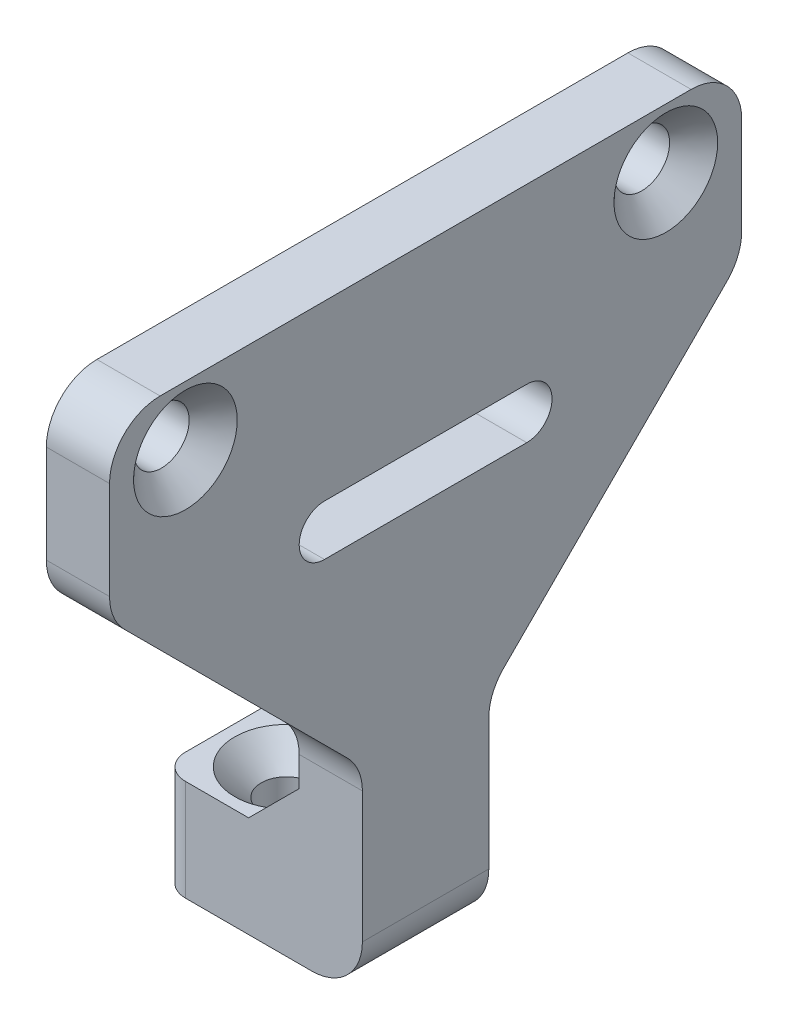
SolidWorks part; units mm, degrees
ref_plane "前视基准面" through (0, 0, 0) normal (0, 0, 1) x (1, 0, 0)
ref_plane "上视基准面" through (0, 0, 0) normal (0, 1, 0) x (1, 0, 0)
ref_plane "右视基准面" through (0, 0, 0) normal (1, 0, 0) x (0, 0, -1)
sketch "草图1" plane through (0, 0, 0) normal (1, 0, 0) x (0, 0, -1)
  line L0 (-12.5, 0) -> (12.5, 0) construction
  line L1 (-12.5, 2.35) -> (12.5, 2.35)
  line L2 (-12.5, 2.35) -> (-12.5, -2.35)
  line L3 (-12.5, -2.35) -> (12.5, -2.35)
  line L4 (12.5, 2.35) -> (12.5, -2.35)
  line L5 (0, -2.35) -> (0, 11.5618) construction
  circle A1 centre (9.5, 0) radius 1.1
  circle A2 centre (-9.5, 0) radius 1.1
  dimension "D3" = 2.2
  dimension "D1" = 9.5
  dimension "D4" = 4.7
  dimension "D5" = 25
  dimension "D6" = 1.9
extrude "凸台-拉伸1" add sketch "草图1" along normal blind 2.5
hole_wizard "M2 平头机械螺钉的锥形沉头孔1" positions "3D草图1" profile "草图2" countersink size "M2" standard "ANSI Metric"
sketch3d "3D草图1"
  line L0 (2.5, 0, 9.5) -> (0, 0, 9.5) construction
  line L1 (2.5, 0, -9.5) -> (0, 0, -9.5) construction
  point P0 (2.5, 0, 9.5)
  point P4 (4.6063, -1.0097, -5.9012)
  point P12 (2.5, 0, -9.5)
sketch "草图2" plane through (2.5, 0, 9.5) normal (0, 1, 0) x (0, 0, -1)
  line L0 (0, 0) -> (0, 2.5)
  line L1 (0, 2.5) -> (1, 2.5)
  line L2 (1, 2.5) -> (1, 1.05)
  line L3 (1, 1.05) -> (2.05, 0)
  line L5 (2.05, 0) -> (0, 0)
  line L6 (-1, 1.05) -> (-2.05, 0) construction
  line L11 (0, -6.35) -> (0, 107.95) construction
  dimension "通孔孔直径" = 2
  dimension "通孔孔深度" = 2.5
  dimension "近端锥形沉头孔直径" = 4.1
  dimension "近端锥形沉头孔角度" = 90
sketch "草图3" plane through (0, 0, 0) normal (0, 0, 1) x (1, 0, 0)
  line L0 (0, -2.35) -> (2.5, -2.35)
  line L1 (2.5, -2.35) -> (2.5, -22.35)
  line L2 (0, -16.35) -> (-2, -18.35)
  line L3 (-2, -18.35) -> (-5.5, -18.35)
  line L4 (0, -2.35) -> (0, -16.35)
  line L5 (-5.5, -18.35) -> (-5.5, -22.35)
  line L6 (-5.5, -22.35) -> (2.5, -22.35)
  line L8 (-3, -27.35) -> (-3, -1.7566) construction
  dimension "D1" = 14
  dimension "D2" = 135
  dimension "D3" = 4
  dimension "D5" = 3
  dimension "D6" = 5.5
  dimension "D7" = 16
extrude "凸台-拉伸2" add sketch "草图3" along normal mid plane 5
sketch "Sketch1" plane through (0, -18.35, 0) normal (0, 1, 0) x (1, 0, 0)
  circle A0 centre (-3, 0) radius 0.85
  dimension "D2" = 1.7
  dimension "D1" = 3
extrude "Extrude1" cut sketch "Sketch1" against normal blind 10
hole_wizard "CSK for M2 Flat Head Machine Screw1" positions "3DSketch1" profile "Sketch2" countersink size "M2" standard "ANSI Metric"
sketch3d "3DSketch1"
  line L0 (-3, -22.35, 0) -> (-3, -18.35, 0) construction
  point P0 (-3, -18.35, 0)
sketch "Sketch2" plane through (-3, -18.35, 0) normal (1, 0, 0) x (0, 0, 1)
  line L0 (0, 0) -> (0, 4)
  line L1 (0, 4) -> (1, 4)
  line L2 (1, 4) -> (1, 1.05)
  line L3 (1, 1.05) -> (2.05, 0)
  line L5 (2.05, 0) -> (0, 0)
  line L6 (-1, 1.05) -> (-2.05, 0) construction
  line L11 (0, -6.35) -> (0, 107.95) construction
  dimension "通孔孔直径" = 2
  dimension "通孔孔深度" = 4
  dimension "近端锥形沉头孔直径" = 4.1
  dimension "近端锥形沉头孔角度" = 90
sketch "Sketch3" plane through (0, -18.35, 0) normal (0, 1, 0) x (1, 0, 0)
  circle A0 centre (-3, 0) radius 2.05
extrude "Extrude2" cut sketch "Sketch3" along normal blind 10
sketch "Sketch6" plane through (2.5, 0, 0) normal (1, 0, 0) x (0, 0, -1)
  line L0 (-12.5, -2.35) -> (-2.5, -2.35)
  line L1 (-2.5, -2.35) -> (-2.5, -14.35)
  line L2 (-2.5, -22.35) -> (-2.5, -2.35) construction
  line L3 (-2.5, -14.35) -> (-12.5, -4.35)
  line L4 (-12.5, -4.35) -> (-12.5, -2.35)
  line L5 (0, 0) -> (0, -12.5066) construction
  line L6 (12.5, -4.35) -> (12.5, -2.35)
  line L7 (2.5, -14.35) -> (12.5, -4.35)
  line L8 (2.5, -2.35) -> (2.5, -14.35)
  line L9 (12.5, -2.35) -> (2.5, -2.35)
  dimension "D1" = 45
  dimension "D2" = 2
extrude "Extrude4" add sketch "Sketch6" against normal up to surface (2.5 mm away) up to face at (0, 0, -10.6)
sketch "Sketch7" plane through (2.5, 0, 0) normal (1, 0, 0) x (0, 0, -1)
  line L0 (-4, -5.5) -> (4, -5.5) construction
  line L1 (-4, -4.5) -> (4, -4.5)
  line L2 (-4, -6.5) -> (4, -6.5)
  line L3 (0, 0) -> (0, -15.7826) construction
  arc A0 (-4, -4.5) -> (-4, -6.5) centre (-4, -5.5) ccw
  arc A1 (4, -6.5) -> (4, -4.5) centre (4, -5.5) ccw
  point P2 (0, -5.5)
  dimension "D1" = 2
  dimension "D2" = 8
  dimension "D3" = 5.5
extrude "Extrude5" cut sketch "Sketch7" against normal blind 10
fillet "Fillet1" radius 2 6 edges at (1.25, -4.35, -12.5) (1.25, -14.35, -2.5) (1.25, -14.35, 2.5) (1.25, -4.35, 12.5) (1.25, 2.35, -12.5) (1.25, 2.35, 12.5)
fillet "Fillet2" radius 1 2 edges at (-5.5, -20.35, -2.5) (-5.5, -20.35, 2.5)
fillet "Fillet3" radius 2 1 edges at (2.5, -22.35, 0)
